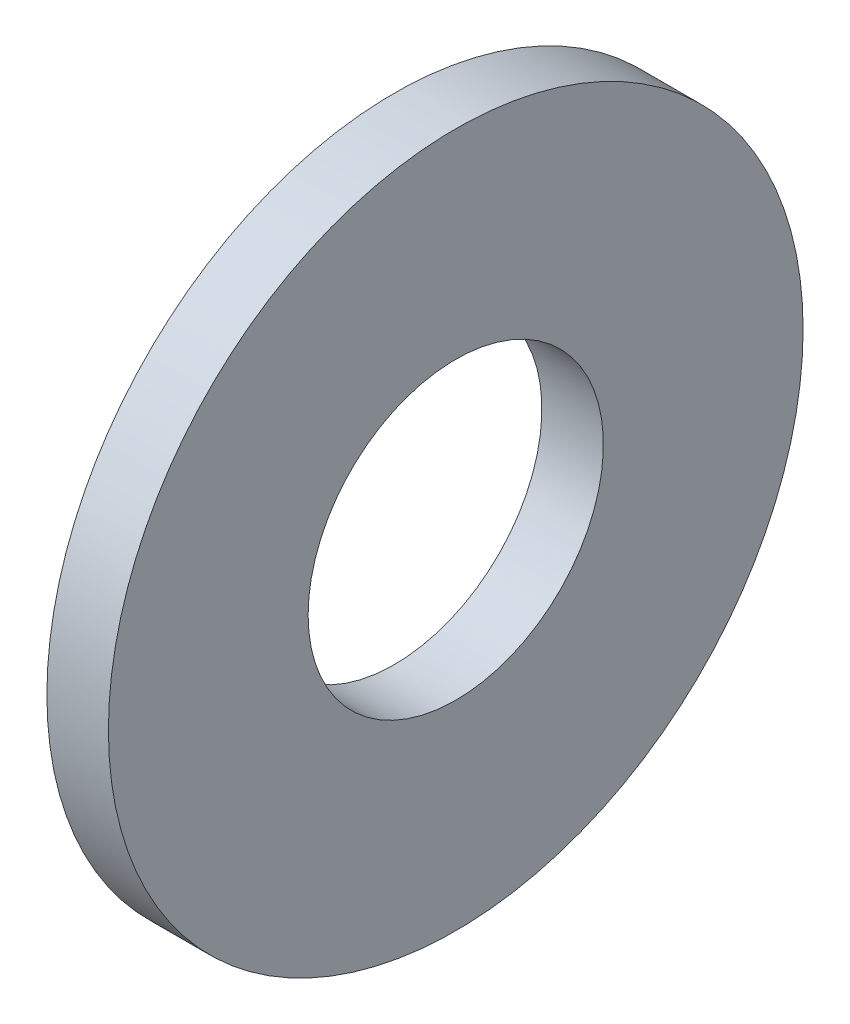
SolidWorks part; units mm, degrees
ref_plane "Plane1" through (0, 0, 0) normal (0, 0, 1) x (1, 0, 0)
ref_plane "Plane2" through (0, 0, 0) normal (0, 1, 0) x (1, 0, 0)
ref_plane "Plane3" through (0, 0, 0) normal (1, 0, 0) x (0, 0, -1)
sketch "Sketch1" plane through (0, 0, 0) normal (0, 0, 1) x (1, 0, 0)
  line L0 (-34.925, 0) -> (9.525, 0) construction
  line L1 (0, 3.9624) -> (0, 9.3218)
  line L2 (0, 9.3218) -> (-1.651, 9.3218)
  line L3 (-1.651, 9.3218) -> (-1.651, 3.9624)
  line L4 (-1.651, 3.9624) -> (0, 3.9624)
  dimension "Thickness" = 1.651
  dimension "Inside_dia" = 7.9248
  dimension "Outside_dia" = 18.6436
revolve "Base-Revolve" add sketch "Sketch1" angle 360 about L0
